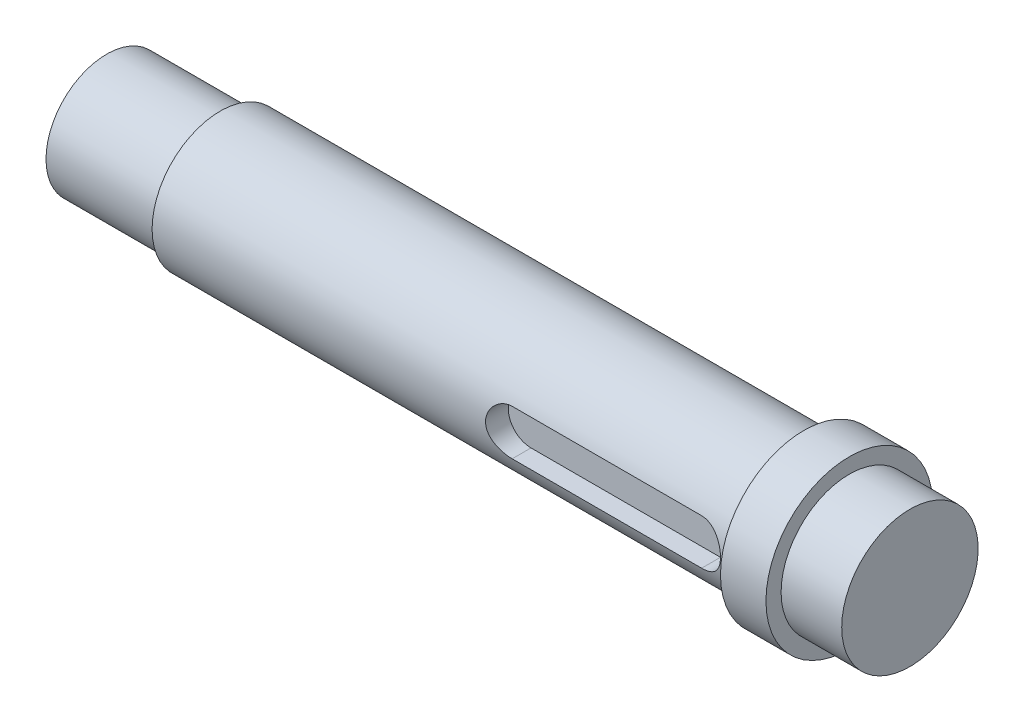
SolidWorks part; units mm, degrees
material "普通碳钢"
ref_plane "前视基准面" through (0, 0, 0) normal (0, 0, 1) x (1, 0, 0)
ref_plane "上视基准面" through (0, 0, 0) normal (0, 1, 0) x (1, 0, 0)
ref_plane "右视基准面" through (0, 0, 0) normal (1, 0, 0) x (0, 0, -1)
sketch "草图2" plane through (0, 0, 0) normal (0, 1, 0) x (1, 0, 0)
  line L0 (0, 0) -> (165.8153, 0) construction
  line L1 (0, 0) -> (0, 8)
  line L2 (15, 9) -> (92, 9)
  line L3 (92, 9) -> (92, 11)
  line L4 (92, 11) -> (98, 11)
  line L5 (15, 9) -> (15, 8)
  line L6 (15, 8) -> (0, 8)
  line L7 (98, 11) -> (98, 9)
  line L8 (98, 9) -> (106, 9)
  line L11 (106, 9) -> (106, 0)
  line L12 (0, 0) -> (106, 0)
  dimension "D1" = 106
  dimension "D2" = 8
  dimension "D3" = 15
  dimension "D4" = 77
  dimension "D5" = 9
  dimension "D6" = 11
  dimension "D7" = 9
  dimension "D8" = 8
  dimension "D9" = 6
revolve "旋转1" add sketch "草图2" angle 360 about L0
cosmetic thread "装饰螺纹线1" parameters "D1"=13, "D2"=13.835
ref_plane "基准面1" through (0, 0, 9) normal (0, 0, 1) x (1, 0, 0)
sketch "草图4" plane through (0, 0, 9) normal (0, 0, 1) x (1, 0, 0)
  line L0 (0, 0) -> (48.9051, 0) construction
  line L1 (62, 0) -> (87, 0) construction
  line L2 (62, 3) -> (87, 3)
  line L3 (62, -3) -> (87, -3)
  line L4 (92, 9) -> (92, -9) construction
  arc A0 (62, 3) -> (62, -3) centre (62, 0) ccw
  arc A1 (87, -3) -> (87, 3) centre (87, 0) ccw
  point P5 (74.5, 0)
  dimension "D1" = 3
  dimension "D2" = 25
  dimension "D3" = 5
extrude "切除-拉伸2" cut sketch "草图4" against normal blind 3
equation "\"16。5\"=23.2"
